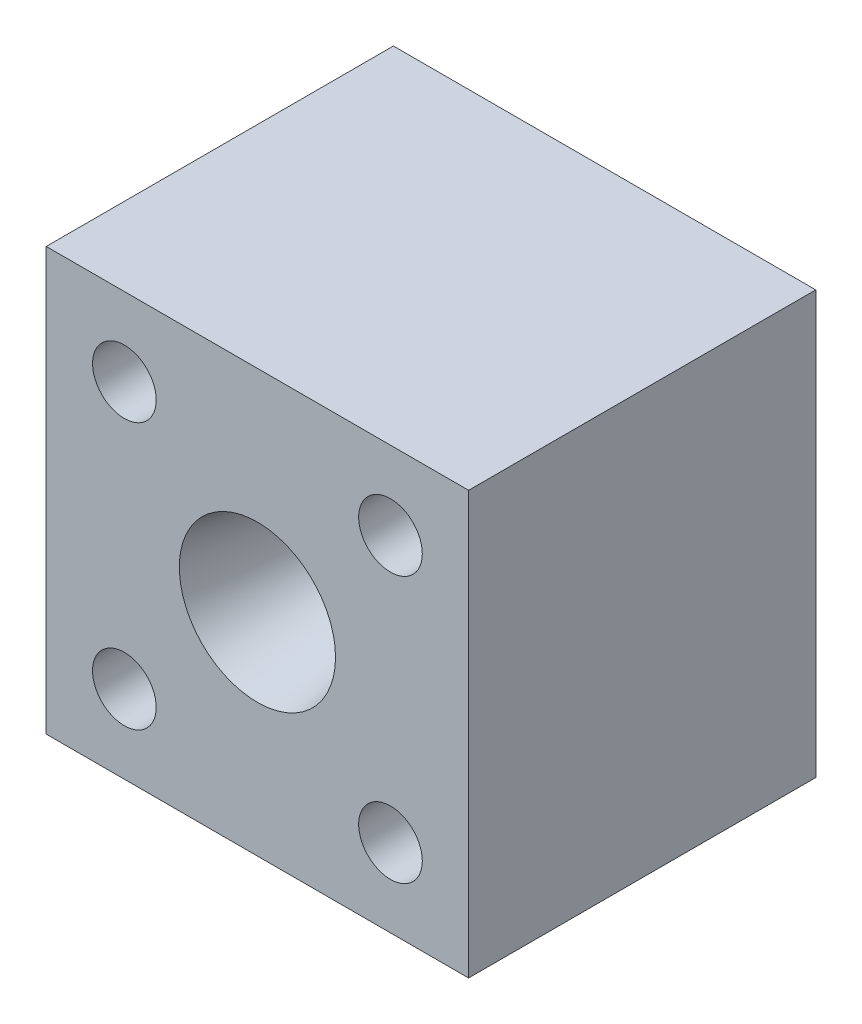
SolidWorks part; units mm, degrees
ref_plane "Front Plane" through (0, 0, 0) normal (0, 0, 1) x (1, 0, 0)
ref_plane "Top Plane" through (0, 0, 0) normal (0, 1, 0) x (1, 0, 0)
ref_plane "Right Plane" through (0, 0, 0) normal (1, 0, 0) x (0, 0, -1)
sketch "Sketch1" plane through (0, 0, 0) normal (0, 0, 1) x (1, 0, 0)
  line L1 (-23.1775, 23.1775) -> (23.1775, 23.1775)
  line L2 (-23.1775, 23.1775) -> (-23.1775, -23.1775)
  line L3 (-23.1775, -23.1775) -> (23.1775, -23.1775)
  line L4 (23.1775, 23.1775) -> (23.1775, -23.1775)
  dimension "D1" = 46.355
  dimension "D2" = 46.355
  dimension "D3" = 23.1775
  dimension "D4" = 23.1775
extrude "Boss-Extrude1" add sketch "Sketch1" along normal blind 63.5
sketch "Sketch2" plane through (0, 0, 63.5) normal (0, 0, 1) x (1, 0, 0)
  circle A0 centre (0, 0) radius 1.27
  dimension "D1" = 2.54
extrude "Cut-Extrude1" cut sketch "Sketch2" against normal through all
sketch "Sketch3" plane through (0, 0, 63.5) normal (0, 0, 1) x (1, 0, 0)
  line L1 (-12.7, 12.7) -> (12.7, 12.7)
  line L2 (-12.7, 12.7) -> (-12.7, -12.7)
  line L3 (-12.7, -12.7) -> (12.7, -12.7)
  line L4 (12.7, 12.7) -> (12.7, -12.7)
  dimension "D1" = 25.4
  dimension "D2" = 25.4
  dimension "D3" = 12.7
  dimension "D4" = 12.7
extrude "Cut-Extrude2" [suppressed] cut sketch "Sketch3" against normal blind 76.2
sketch "Sketch4" plane through (0, 0, 63.5) normal (0, 0, 1) x (1, 0, 0)
  line L0 (0, 0) -> (30.5635, 0) construction
  line L1 (0, 0) -> (25.1205, 25.1205) construction
  circle A0 centre (14.6019, 14.6019) radius 3.4925
  dimension "D3" = 6.985
  dimension "D1" = 20.6502
  dimension "D2" = 45
extrude "Cut-Extrude3" cut sketch "Sketch4" against normal through all
mirror "Mirror1" about plane through (0, 0, 0) normal (0, 1, 0) of "Cut-Extrude3"
mirror "Mirror2" about plane through (0, 0, 0) normal (1, 0, 0) of "Mirror1", "Cut-Extrude3"
sketch "Sketch5" plane through (0, 0, 0) normal (1, 0, 0) x (0, 0, -1)
  line L0 (-63.5, 9.7136) -> (-44.0579, 9.7136)
  line L1 (-63.5, -23.1775) -> (-63.5, 23.1775) construction
  line L2 (-44.0579, 9.7136) -> (0, 1.27)
  line L3 (0, -23.1775) -> (0, 23.1775) construction
  line L4 (0, 1.27) -> (0, 0)
  line L5 (0, 0) -> (-63.5, 0)
  line L6 (-63.5, 0) -> (-63.5, 9.7136)
  dimension "D1" = 1.27
revolve "Cut-Revolve1" cut sketch "Sketch5" angle 360 about L5
sketch "Sketch6" plane through (0, 0, 63.5) normal (0, 0, 1) x (1, 0, 0)
  line L1 (-25.0386, 25.3849) -> (25.6013, 25.3849)
  line L2 (-25.0386, 25.3849) -> (-25.0386, -25.9475)
  line L3 (-25.0386, -25.9475) -> (25.6013, -25.9475)
  line L4 (25.6013, 25.3849) -> (25.6013, -25.9475)
extrude "Cut-Extrude4" cut sketch "Sketch6" against normal offset from surface (25.4 mm away) 38.1 up to face at (-18.0944, -14.6019, 0)
equation "\"D4@Sketch1\"=\"D1@Sketch1\"/2"
equation "\"D3@Sketch1\"=\"D2@Sketch1\"/2"
equation "\"D2@Sketch3\"=\"D1@Sketch3\""
equation "\"D3@Sketch3\"=\"D2@Sketch3\"/2"
equation "\"D4@Sketch3\"=\"D1@Sketch3\"/2"
equation "\"D2@Sketch1\"=\"D1@Sketch1\""
